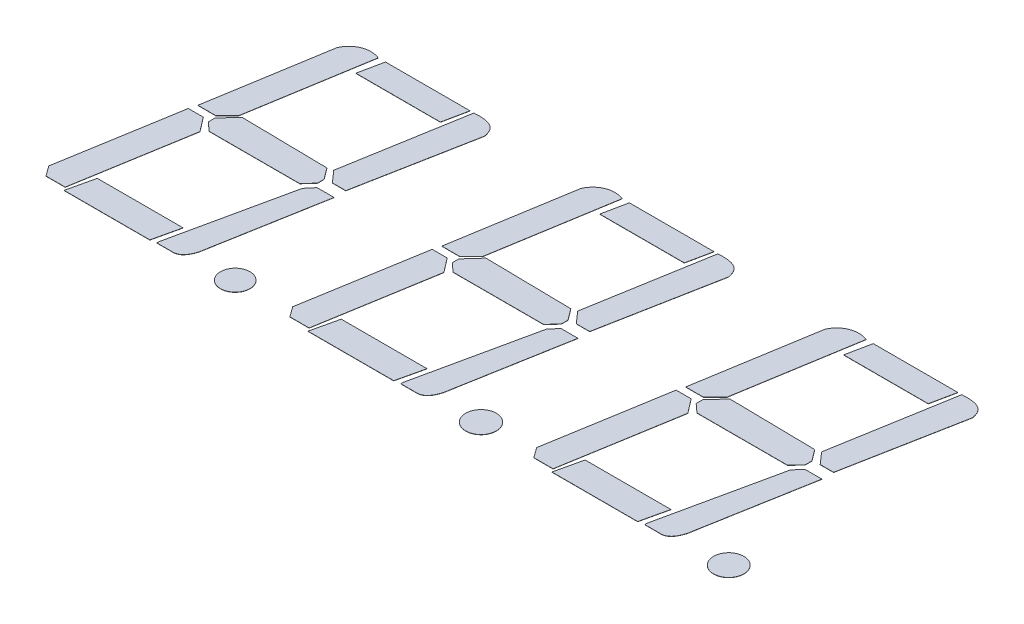
SolidWorks part; units mm, degrees
ref_plane "Front" through (0, 0, 0) normal (0, 0, 1) x (1, 0, 0)
ref_plane "Top" through (0, 0, 0) normal (0, 1, 0) x (1, 0, 0)
ref_plane "Right" through (0, 0, 0) normal (1, 0, 0) x (0, 0, -1)
sketch "Эскиз1" plane through (0, 0, 0) normal (0, 1, 0) x (1, 0, 0)
  line L1 (-18.8794, 8.182) -> (18.9862, 8.182) construction
  line L2 (-18.8794, 8.182) -> (-18.8794, -10.7301) construction
  line L3 (-18.8794, -10.7301) -> (18.9862, -10.7301) construction
  line L4 (18.9862, 8.182) -> (18.9862, -10.7301) construction
  line L5 (-25, -18.9623) -> (25, 18.9623) construction
  line L6 (-25, 18.9623) -> (25, -18.9623) construction
  circle A0 centre (-7.6586, -7.8168) radius 0.7634
  circle A1 centre (5.0886, -7.8168) radius 0.7951
  circle A2 centre (17.9354, -7.8168) radius 0.7876
  point P0 (0, 0)
  line B0 (-13.9354, 5.8775) -> (-14.9533, -0.3253)
  line B1 (-14.9533, -0.3253) -> (-15.5577, -0.9297)
  line B2 (-15.5577, -0.9297) -> (-16.4802, -0.9297)
  line B3 (-16.4802, -0.9297) -> (-15.4648, 5.2579)
  line B4 (-13.5611, 5.8775) -> (-13.8242, 4.6054)
  line B5 (-13.8242, 4.6054) -> (-9.4388, 4.6054)
  line B6 (-9.4388, 4.6054) -> (-9.1757, 5.8775)
  line B7 (-9.1757, 5.8775) -> (-13.5611, 5.8775)
  line B8 (-8.9765, 5.8775) -> (-10.0398, -0.3253)
  line B9 (-10.0398, -0.3253) -> (-9.5081, -0.9297)
  line B10 (-9.5081, -0.9297) -> (-8.8118, -0.9297)
  line B11 (-8.8118, -0.9297) -> (-7.6586, 5.1425)
  line B12 (-14.7964, -0.3253) -> (-15.4648, -1.0636)
  line B13 (-15.4648, -1.0636) -> (-15.4648, -1.4047)
  line B14 (-15.4648, -1.4047) -> (-15.0208, -1.8066)
  line B15 (-15.0208, -1.8066) -> (-10.3217, -1.8066)
  line B16 (-10.3217, -1.8066) -> (-9.8838, -1.3229)
  line B17 (-9.8838, -1.3229) -> (-9.8838, -0.9827)
  line B18 (-9.8838, -0.9827) -> (-10.3217, -0.3987)
  line B19 (-10.3217, -0.3987) -> (-14.7964, -0.3253)
  line B20 (-15.8081, -6.8192) -> (-16.1296, -8.2213)
  line B21 (-16.1296, -8.2213) -> (-11.6822, -8.2213)
  line B22 (-11.6822, -8.2213) -> (-11.3607, -6.8192)
  line B23 (-11.3607, -6.8192) -> (-15.8081, -6.8192)
  line B24 (-16.5863, -1.3229) -> (-17.6231, -7.5203)
  line B25 (-16.5863, -1.3229) -> (-15.8081, -1.3229)
  line B26 (-15.8081, -1.3229) -> (-15.2445, -2.0583)
  line B27 (-15.2445, -2.0583) -> (-16.2463, -8.0463)
  line B28 (-16.2463, -8.0463) -> (-17.242, -8.0463)
  line B29 (-17.242, -8.0463) -> (-17.6231, -7.5203)
  line B30 (-11.3607, -8.0463) -> (-10.0398, -1.9516)
  line B31 (-10.0398, -1.9516) -> (-9.6944, -1.5399)
  line B32 (-9.6944, -1.5399) -> (-8.8118, -1.5399)
  line B33 (-8.8118, -1.5399) -> (-9.8671, -7.4841)
  line B34 (-11.3607, -8.0463) -> (-11.3607, -8.1741)
  line B35 (-11.3607, -8.1741) -> (-10.6089, -8.1741)
  spline B36 degree 3 poles (-13.9354, 5.8775) (-14.6104, 6.1385) (-15.2378, 5.8083) (-15.4648, 5.2579) knots 0 0 0 0 0.625518 0.625518 0.625518 0.625518
  spline B37 degree 3 poles (-8.9765, 5.8775) (-7.7898, 5.9714) (-7.7541, 5.437) (-7.6586, 5.1425) knots 0 0 0 0 0.497851 0.497851 0.497851 0.497851
  spline B38 degree 3 poles (-9.8671, -7.4841) (-10.0194, -7.9659) (-10.2395, -8.2037) (-10.6089, -8.1741) knots 0 0 0 0 1 1 1 1
  line B39 (-1.2854, 5.8775) -> (-2.3033, -0.3253)
  line B40 (-2.3033, -0.3253) -> (-2.9077, -0.9297)
  line B41 (-2.9077, -0.9297) -> (-3.8302, -0.9297)
  line B42 (-3.8302, -0.9297) -> (-2.8148, 5.2579)
  line B43 (-0.9111, 5.8775) -> (-1.1742, 4.6054)
  line B44 (-1.1742, 4.6054) -> (3.2112, 4.6054)
  line B45 (3.2112, 4.6054) -> (3.4743, 5.8775)
  line B46 (3.4743, 5.8775) -> (-0.9111, 5.8775)
  line B47 (3.6735, 5.8775) -> (2.6102, -0.3253)
  line B48 (2.6102, -0.3253) -> (3.1419, -0.9297)
  line B49 (3.1419, -0.9297) -> (3.8382, -0.9297)
  line B50 (3.8382, -0.9297) -> (4.9914, 5.1425)
  line B51 (-2.1464, -0.3253) -> (-2.8148, -1.0636)
  line B52 (-2.8148, -1.0636) -> (-2.8148, -1.4047)
  line B53 (-2.8148, -1.4047) -> (-2.3708, -1.8066)
  line B54 (-2.3708, -1.8066) -> (2.3283, -1.8066)
  line B55 (2.3283, -1.8066) -> (2.7662, -1.3229)
  line B56 (2.7662, -1.3229) -> (2.7662, -0.9827)
  line B57 (2.7662, -0.9827) -> (2.3283, -0.3987)
  line B58 (2.3283, -0.3987) -> (-2.1464, -0.3253)
  line B59 (-3.1581, -6.8192) -> (-3.4796, -8.2213)
  line B60 (-3.4796, -8.2213) -> (0.9678, -8.2213)
  line B61 (0.9678, -8.2213) -> (1.2893, -6.8192)
  line B62 (1.2893, -6.8192) -> (-3.1581, -6.8192)
  line B63 (-3.9363, -1.3229) -> (-4.9731, -7.5203)
  line B64 (-3.9363, -1.3229) -> (-3.1581, -1.3229)
  line B65 (-3.1581, -1.3229) -> (-2.5945, -2.0583)
  line B66 (-2.5945, -2.0583) -> (-3.5963, -8.0463)
  line B67 (-3.5963, -8.0463) -> (-4.592, -8.0463)
  line B68 (-4.592, -8.0463) -> (-4.9731, -7.5203)
  line B69 (1.2893, -8.0463) -> (2.6102, -1.9516)
  line B70 (2.6102, -1.9516) -> (2.9556, -1.5399)
  line B71 (2.9556, -1.5399) -> (3.8382, -1.5399)
  line B72 (3.8382, -1.5399) -> (2.7829, -7.4841)
  line B73 (1.2893, -8.0463) -> (1.2893, -8.1741)
  line B74 (1.2893, -8.1741) -> (2.0411, -8.1741)
  spline B75 degree 3 poles (-1.2854, 5.8775) (-1.9604, 6.1385) (-2.5878, 5.8083) (-2.8148, 5.2579) knots 0 0 0 0 0.625518 0.625518 0.625518 0.625518
  spline B76 degree 3 poles (3.6735, 5.8775) (4.8602, 5.9714) (4.8959, 5.437) (4.9914, 5.1425) knots 0 0 0 0 0.497851 0.497851 0.497851 0.497851
  spline B77 degree 3 poles (2.7829, -7.4841) (2.6306, -7.9659) (2.4105, -8.2037) (2.0411, -8.1741) knots 0 0 0 0 1 1 1 1
  line B78 (11.3646, 5.8775) -> (10.3467, -0.3253)
  line B79 (10.3467, -0.3253) -> (9.7423, -0.9297)
  line B80 (9.7423, -0.9297) -> (8.8198, -0.9297)
  line B81 (8.8198, -0.9297) -> (9.8352, 5.2579)
  line B82 (11.7389, 5.8775) -> (11.4758, 4.6054)
  line B83 (11.4758, 4.6054) -> (15.8612, 4.6054)
  line B84 (15.8612, 4.6054) -> (16.1243, 5.8775)
  line B85 (16.1243, 5.8775) -> (11.7389, 5.8775)
  line B86 (16.3235, 5.8775) -> (15.2602, -0.3253)
  line B87 (15.2602, -0.3253) -> (15.7919, -0.9297)
  line B88 (15.7919, -0.9297) -> (16.4882, -0.9297)
  line B89 (16.4882, -0.9297) -> (17.6414, 5.1425)
  line B90 (10.5036, -0.3253) -> (9.8352, -1.0636)
  line B91 (9.8352, -1.0636) -> (9.8352, -1.4047)
  line B92 (9.8352, -1.4047) -> (10.2792, -1.8066)
  line B93 (10.2792, -1.8066) -> (14.9783, -1.8066)
  line B94 (14.9783, -1.8066) -> (15.4162, -1.3229)
  line B95 (15.4162, -1.3229) -> (15.4162, -0.9827)
  line B96 (15.4162, -0.9827) -> (14.9783, -0.3987)
  line B97 (14.9783, -0.3987) -> (10.5036, -0.3253)
  line B98 (9.4919, -6.8192) -> (9.1704, -8.2213)
  line B99 (9.1704, -8.2213) -> (13.6178, -8.2213)
  line B100 (13.6178, -8.2213) -> (13.9393, -6.8192)
  line B101 (13.9393, -6.8192) -> (9.4919, -6.8192)
  line B102 (8.7137, -1.3229) -> (7.6769, -7.5203)
  line B103 (8.7137, -1.3229) -> (9.4919, -1.3229)
  line B104 (9.4919, -1.3229) -> (10.0555, -2.0583)
  line B105 (10.0555, -2.0583) -> (9.0537, -8.0463)
  line B106 (9.0537, -8.0463) -> (8.058, -8.0463)
  line B107 (8.058, -8.0463) -> (7.6769, -7.5203)
  line B108 (13.9393, -8.0463) -> (15.2602, -1.9516)
  line B109 (15.2602, -1.9516) -> (15.6056, -1.5399)
  line B110 (15.6056, -1.5399) -> (16.4882, -1.5399)
  line B111 (16.4882, -1.5399) -> (15.4329, -7.4841)
  line B112 (13.9393, -8.0463) -> (13.9393, -8.1741)
  line B113 (13.9393, -8.1741) -> (14.6911, -8.1741)
  spline B114 degree 3 poles (11.3646, 5.8775) (10.6896, 6.1385) (10.0622, 5.8083) (9.8352, 5.2579) knots 0 0 0 0 0.625518 0.625518 0.625518 0.625518
  spline B115 degree 3 poles (16.3235, 5.8775) (17.5102, 5.9714) (17.5459, 5.437) (17.6414, 5.1425) knots 0 0 0 0 0.497851 0.497851 0.497851 0.497851
  spline B116 degree 3 poles (15.4329, -7.4841) (15.2806, -7.9659) (15.0605, -8.2037) (14.6911, -8.1741) knots 0 0 0 0 1 1 1 1
  dimension "D1" = 50
  dimension "D2" = 3
sketch_block_instance "Блок1-1"
sketch_block "Блок1"
sketch_block_instance "Блок1-2"
sketch_block_instance "Блок1-3"
extrude "Бобышка-Вытянуть1" add sketch "Эскиз1" along normal blind 0.01
